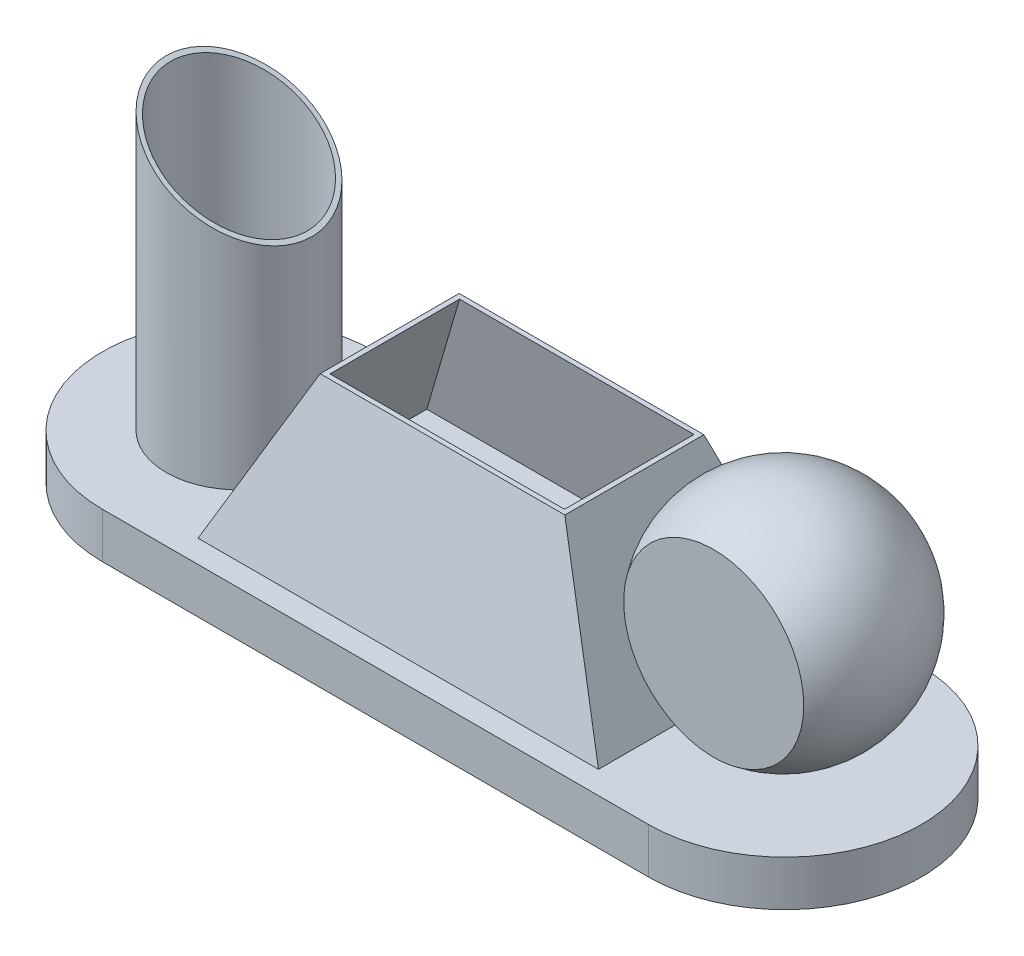
SolidWorks part; units mm, degrees
ref_plane "Front Plane" through (0, 0, 0) normal (0, 0, 1) x (1, 0, 0)
ref_plane "Top Plane" through (0, 0, 0) normal (0, 1, 0) x (1, 0, 0)
ref_plane "Right Plane" through (0, 0, 0) normal (1, 0, 0) x (0, 0, -1)
sketch "Sketch1" plane through (0, 0, 0) normal (0, 1, 0) x (1, 0, 0)
  line L0 (-60, 0) -> (60, 0) construction
  line L1 (-60, 30) -> (60, 30)
  line L2 (-60, -30) -> (60, -30)
  arc A0 (-60, 30) -> (-60, -30) centre (-60, 0) ccw
  arc A1 (60, -30) -> (60, 30) centre (60, 0) ccw
  point P2 (0, 0)
  dimension "D1" = 30
  dimension "D2" = 60
extrude "Extrude1" add sketch "Sketch1" along normal blind 10
sketch "Sketch2" plane through (0, 10, 0) normal (0, 1, 0) x (1, 0, 0)
  line L1 (-44, 25) -> (44, 25)
  line L2 (-44, 25) -> (-44, -25)
  line L3 (-44, -25) -> (44, -25)
  line L4 (44, 25) -> (44, -25)
  line L5 (-44, 25) -> (44, -25) construction
  line L6 (-44, -25) -> (44, 25) construction
  point P0 (0, 0)
  dimension "D1" = 88
  dimension "D2" = 50
sketch "Sketch3" plane through (0, 0, 0) normal (0, 0, 1) x (1, 0, 0)
  line L0 (0, 10) -> (0, 100) construction
  point P0 (0, 100)
  dimension "D1" = 90
loft "Loft1" add profiles "Sketch2", "Sketch3"
sketch "Sketch4" plane through (0, 0, 0) normal (0, 0, 1) x (1, 0, 0)
  line L0 (-44, 10) -> (44, 10) construction
  line L1 (-46.4512, 45) -> (38.0403, 45)
  line L2 (-46.4512, 45) -> (-46.4512, 107.3173)
  line L3 (-46.4512, 107.3173) -> (38.0403, 107.3173)
  line L4 (38.0403, 45) -> (38.0403, 107.3173)
  dimension "D1" = 35
extrude "Extrude2" cut sketch "Sketch4" against normal mid plane 50
shell "Shell1" thickness 1
sketch "Sketch5" plane through (0, 10, 0) normal (0, 1, 0) x (1, 0, 0)
  circle A0 centre (-60, 0) radius 16
extrude "Extrude3" add sketch "Sketch5" along normal blind 90 separate body
sketch "Sketch7" plane through (0, 0, 0) normal (0, 0, 1) x (1, 0, 0)
  line L0 (-26.8889, 45) -> (-97.3263, 85.667)
  line L1 (-97.3263, 85.667) -> (-97.3263, 110.8998)
  line L2 (-97.3263, 110.8998) -> (-26.8889, 110.8998)
  line L3 (-26.8889, 110.8998) -> (-26.8889, 45)
  dimension "D1" = 60
extrude "Extrude4" cut sketch "Sketch7" against normal mid plane 90
shell "Shell2" thickness 1
sketch "Sketch8" plane through (0, 0, 0) normal (0, 0, 1) x (1, 0, 0)
  line L0 (90, 10) -> (60, 10) construction
  line L1 (44, 10) -> (26.8889, 45) construction
  line L2 (59.6055, 60) -> (59.6055, 10)
  arc A0 (59.6055, 60) -> (59.6055, 10) centre (59.6055, 35) ccw
  dimension "D1" = 50
revolve "Revolve1" add sketch "Sketch8" angle 360 about L2
ref_plane "Plane1" through (0, 0, 15.2778) normal (0, 0, 1) x (1, 0, 0)
sketch "Sketch10" plane through (0, 0, 15.2778) normal (0, 0, 1) x (1, 0, 0)
  line L0 (59.6055, 60) -> (59.6055, 10) construction
  line L1 (-60, 10) -> (60, 10) construction
  circle A0 centre (59.6055, 35) radius 25 construction
  circle A1 centre (59.6055, 35) radius 25
  dimension "D1" = 50
extrude "Extrude5" cut sketch "Sketch10" along normal blind 90
